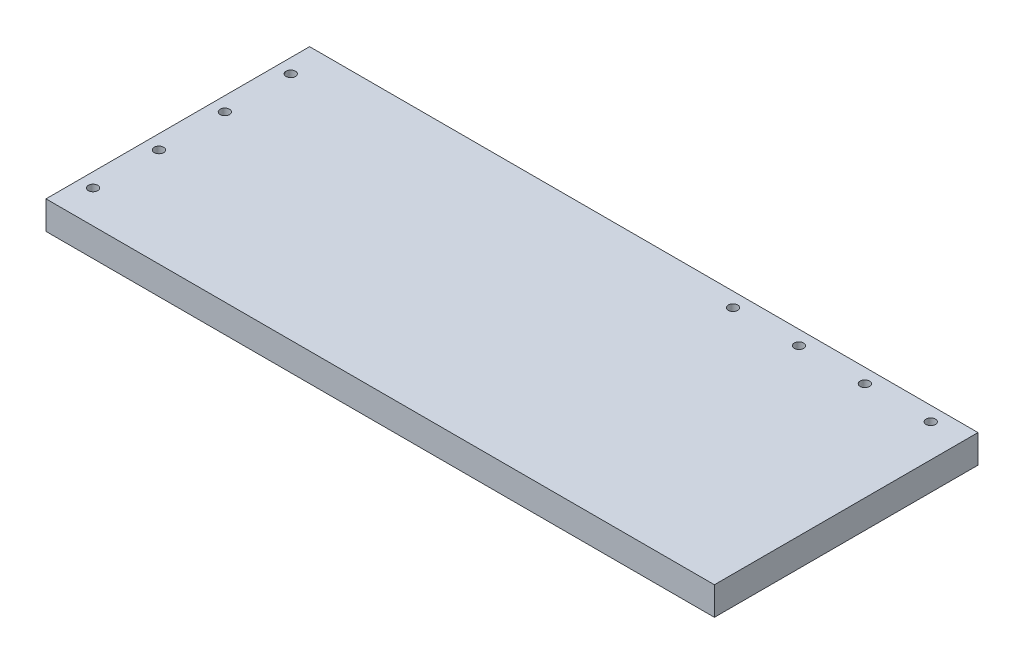
SolidWorks part; units mm, degrees
material "Pine"
ref_plane "Front Plane" through (0, 0, 0) normal (0, 0, 1) x (1, 0, 0)
ref_plane "Top Plane" through (0, 0, 0) normal (0, 1, 0) x (1, 0, 0)
ref_plane "Right Plane" through (0, 0, 0) normal (1, 0, 0) x (0, 0, -1)
sketch "Sketch1" plane through (0, 0, 0) normal (0, 1, 0) x (1, 0, 0)
  line L1 (-225.425, 88.9) -> (225.425, 88.9)
  line L2 (-225.425, 88.9) -> (-225.425, -88.9)
  line L3 (-225.425, -88.9) -> (225.425, -88.9)
  line L4 (225.425, 88.9) -> (225.425, -88.9)
  line L5 (-225.425, 88.9) -> (225.425, -88.9) construction
  line L6 (-225.425, -88.9) -> (225.425, 88.9) construction
  point P0 (0, 0)
  dimension "D1" = 450.85
  dimension "D2" = 177.8
extrude "Boss-Extrude1" add sketch "Sketch1" along normal mid plane 19.05
hole_wizard "1/4 (0.25) Diameter Hole2" positions "Sketch7" profile "Sketch6" hole size "1/4" standard "ANSI Inch"
sketch "Sketch7" plane through (0, 9.525, 0) normal (0, 1, 0) x (1, 0, 0)
  line L0 (225.425, 88.9) -> (-225.425, 88.9) construction
  line L1 (-225.425, 88.9) -> (-225.425, -88.9) construction
  point P0 (-215.9, 66.675)
  point P2 (-215.9, 22.225)
  point P4 (-215.9, -22.225)
  point P6 (-215.9, -66.675)
  dimension "D1" = 22.225
  dimension "D2" = 44.45
  dimension "D3" = 44.45
  dimension "D4" = 44.45
  dimension "D5" = 9.525
sketch "Sketch6" plane through (-215.9, 9.525, -66.675) normal (1, 0, 0) x (0, 0, 1)
  line L0 (0, 0) -> (0, 27.3077)
  line L1 (0, 27.3077) -> (3.175, 25.4)
  line L2 (3.175, 25.4) -> (3.175, 0)
  line L5 (3.175, 0) -> (0, 0)
  line L10 (0, 27.3077) -> (-3.175, 25.4) construction
  line L11 (0, -6.35) -> (0, 107.95) construction
  dimension "Hole Dia." = 6.35
  dimension "Hole Depth" = 25.4
  dimension "Drill Angle" = 118
hole_wizard "1/4 (0.25) Diameter Hole3" positions "Sketch11" profile "Sketch10" hole size "1/4" standard "ANSI Inch"
sketch "Sketch11" plane through (0, 9.525, 0) normal (0, 1, 0) x (1, 0, 0)
  line L0 (225.425, -88.9) -> (225.425, 88.9) construction
  line L1 (225.425, 88.9) -> (-225.425, 88.9) construction
  point P0 (203.2, 79.248)
  point P2 (158.75, 79.248)
  point P4 (114.3, 79.248)
  point P6 (69.85, 79.248)
  dimension "D1" = 22.225
  dimension "D2" = 44.45
  dimension "D3" = 44.45
  dimension "D4" = 44.45
  dimension "D5" = 9.652
sketch "Sketch10" plane through (203.2, 9.525, -79.248) normal (1, 0, 0) x (0, 0, 1)
  line L0 (0, 0) -> (0, 27.3077)
  line L1 (0, 27.3077) -> (3.175, 25.4)
  line L2 (3.175, 25.4) -> (3.175, 0)
  line L5 (3.175, 0) -> (0, 0)
  line L10 (0, 27.3077) -> (-3.175, 25.4) construction
  line L11 (0, -6.35) -> (0, 107.95) construction
  dimension "Hole Dia." = 6.35
  dimension "Hole Depth" = 25.4
  dimension "Drill Angle" = 118
